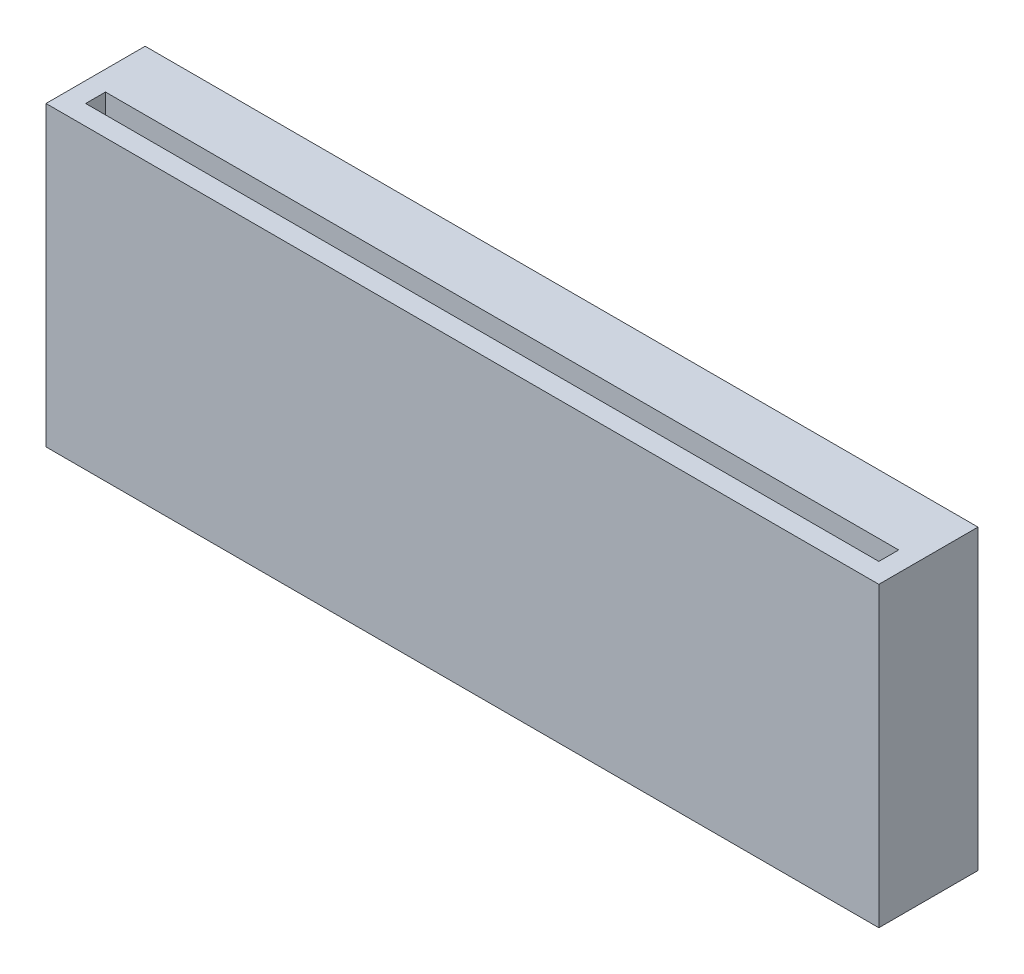
SolidWorks part; units mm, degrees
ref_plane "Front Plane" through (0, 0, 0) normal (0, 0, 1) x (1, 0, 0)
ref_plane "Top Plane" through (0, 0, 0) normal (0, 1, 0) x (1, 0, 0)
ref_plane "Right Plane" through (0, 0, 0) normal (1, 0, 0) x (0, 0, -1)
sketch "Sketch1" plane through (0, 0, 0) normal (0, 0, 1) x (1, 0, 0)
  line L1 (0, 0) -> (-40, 0)
  line L2 (0, 0) -> (0, 15)
  line L3 (0, 15) -> (-40, 15)
  line L4 (-40, 0) -> (-40, 15)
  dimension "D1" = 40
  dimension "D2" = 15
extrude "Boss-Extrude1" add sketch "Sketch1" along normal blind 5
sketch "Sketch2" plane through (0, 0, 0) normal (0, -1, 0) x (1, 0, 0)
  line L0 (-40, 0) -> (0, 0) construction
  line L1 (-8, 0) -> (-12, 0)
  line L2 (-8, 0) -> (-8, -2.5)
  line L4 (-12, 0) -> (-12, -2.5)
  line L5 (0, 5) -> (0, 0) construction
  line L11 (-8, -2.5) -> (-5.5, -2.5)
  line L12 (-5.5, -2.5) -> (-5.5, -3.5)
  line L13 (-5.5, -3.5) -> (-8, -6)
  line L14 (-8, -6) -> (-12, -6)
  line L15 (-12, -6) -> (-14.5, -3.5)
  line L16 (-14.5, -3.5) -> (-14.5, -2.5)
  line L17 (-14.5, -2.5) -> (-12, -2.5)
  point P20 (0, 0)
  point P21 (0, 0)
  point P22 (0, 0)
  point P23 (-8, -5.944)
  dimension "D2" = 4
  dimension "D4" = 2.5
  dimension "D5" = 8
  dimension "D7" = 1
  dimension "D8" = 1
  dimension "D9" = 2.5
  dimension "D10" = 2.5
extrude "Boss-Extrude2" add sketch "Sketch2" against normal blind 7.5
ref_plane "Plane1" through (-20, 0, 0) normal (1, 0, 0) x (0, 0, -1)
mirror "Mirror1" about plane through (-20, 0, 0) normal (1, 0, 0) of "Boss-Extrude2"
sketch "Sketch3" plane through (0, 0, 0) normal (1, 0, 0) x (0, 0, -1)
  line L0 (-5, 0) -> (-5, 15) construction
  line L1 (0, 0) -> (-5, 0)
  line L2 (0, 0) -> (0, 15)
  line L3 (0, 15) -> (-5, 15)
  line L4 (-5, 0) -> (-5, 15)
  line L5 (-5, 15) -> (0, 15) construction
extrude "Boss-Extrude3" add sketch "Sketch3" along normal blind 1
mirror "Mirror2" about plane through (-20, 0, 0) normal (1, 0, 0) of "Boss-Extrude3"
sketch "Sketch4" plane through (0, 15, 0) normal (0, 1, 0) x (1, 0, 0)
  line L0 (1, -5) -> (-41, -5) construction
  line L1 (0, -3) -> (-40, -3)
  line L2 (0, -3) -> (0, -4)
  line L3 (0, -4) -> (-40, -4)
  line L4 (-40, -3) -> (-40, -4)
  line L5 (1, 0) -> (1, -5) construction
  line L6 (-41, 0) -> (-41, -5) construction
  dimension "D1" = 1
  dimension "D2" = 1
  dimension "D3" = 1
  dimension "D4" = 1
extrude "Cut-Extrude1" cut sketch "Sketch4" against normal blind 12
